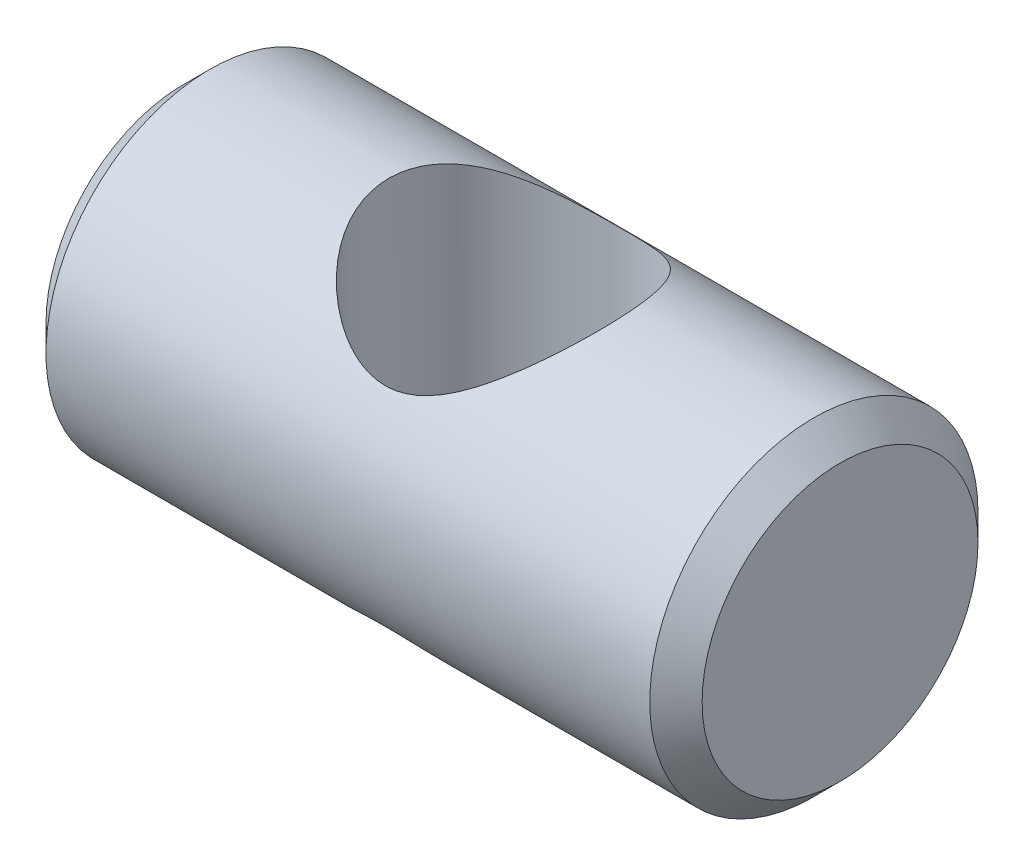
SolidWorks part; units mm, degrees
ref_plane "Alzado" through (0, 0, 0) normal (0, 0, 1) x (1, 0, 0)
ref_plane "Planta" through (0, 0, 0) normal (0, 1, 0) x (1, 0, 0)
ref_plane "Vista lateral" through (0, 0, 0) normal (1, 0, 0) x (0, 0, -1)
sketch "Croquis1" plane through (0, 0, 0) normal (1, 0, 0) x (0, 0, -1)
  circle A0 centre (0, 0) radius 4.765
  dimension "D1" = 9.53
extrude "Saliente-Extruir1" add sketch "Croquis1" along normal mid plane 19.05
chamfer "Chaflán1" distance 0.76 angle 45 2 edges at (-9.525, 0, -4.765) (9.525, 0, -4.765)
sketch "Croquis2" plane through (0, 0, 0) normal (0, 1, 0) x (1, 0, 0)
  circle A0 centre (0, -0.25) radius 3.43
  point P2 (0, 0)
  dimension "D1" = 0.25
  dimension "D2" = 6.86
extrude "Cortar-Extruir1" cut sketch "Croquis2" against normal through all both and the other way through all
